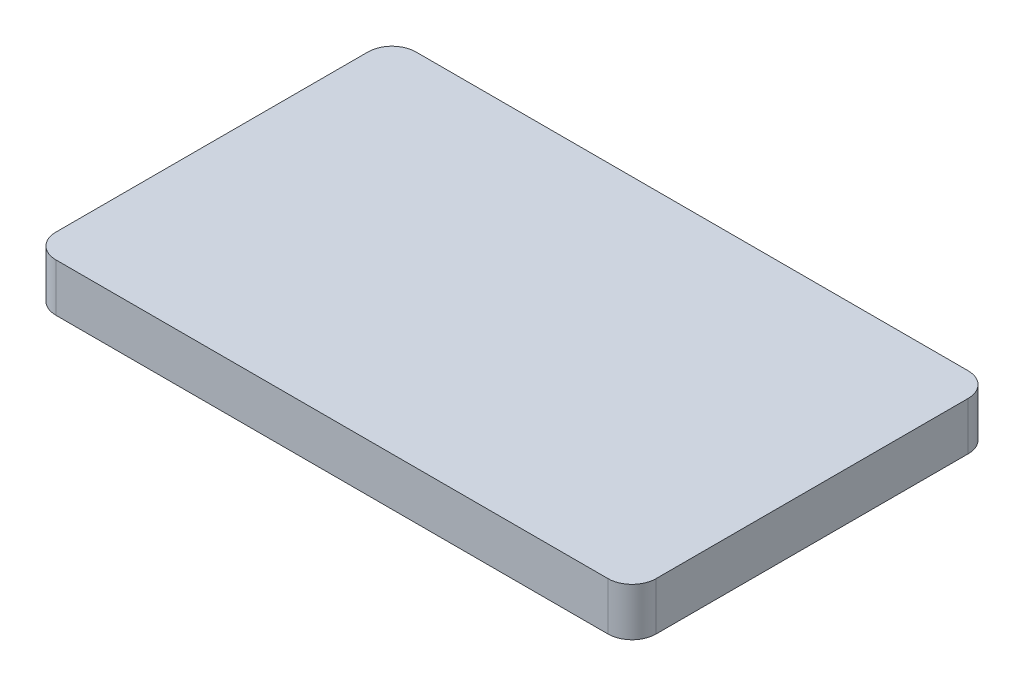
SolidWorks part; units mm, degrees
ref_plane "Front" through (0, 0, 0) normal (0, 0, 1) x (1, 0, 0)
ref_plane "Top" through (0, 0, 0) normal (0, 1, 0) x (1, 0, 0)
ref_plane "Right" through (0, 0, 0) normal (1, 0, 0) x (0, 0, -1)
sketch "草图1" plane through (0, 0, 0) normal (0, 1, 0) x (1, 0, 0)
  line L1 (-125, -75) -> (125, -75)
  line L2 (-125, -75) -> (-125, 75)
  line L3 (-125, 75) -> (125, 75)
  line L4 (125, -75) -> (125, 75)
  line L5 (-125, -75) -> (125, 75) construction
  line L6 (-125, 75) -> (125, -75) construction
  point P0 (0, 0)
  dimension "D1" = 250
  dimension "D2" = 150
extrude "凸台-拉伸1" add sketch "草图1" along normal blind 20
fillet "圆角1" radius 10 4 edges at (-125, 10, -75) (125, 10, -75) (125, 10, 75) (-125, 10, 75)
